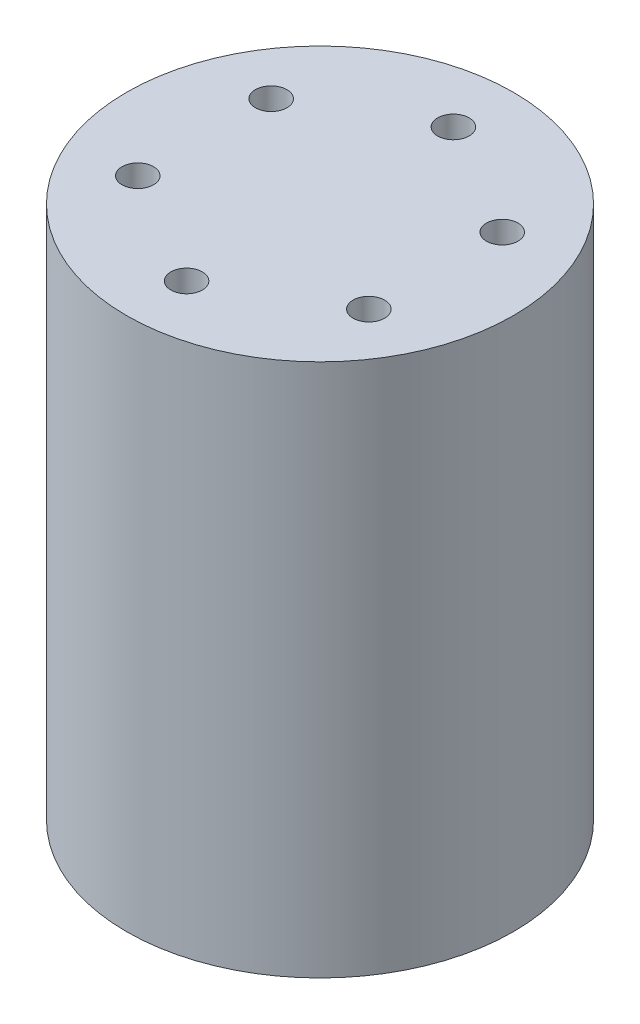
SolidWorks part; units mm, degrees
ref_plane "Front Plane" through (0, 0, 0) normal (0, 0, 1) x (1, 0, 0)
ref_plane "Top Plane" through (0, 0, 0) normal (0, 1, 0) x (1, 0, 0)
ref_plane "Right Plane" through (0, 0, 0) normal (1, 0, 0) x (0, 0, -1)
other "Bounding Box"
ref_plane "Default Plane" through (13.8565, 3.175, 6.7999) normal (0, -1, 0) x (-1, 0, 0)
sketch "Sketch1" plane through (0, 0, 0) normal (0, 1, 0) x (1, 0, 0)
  circle A0 centre (0, 0) radius 18.415
  dimension "D1" = 36.83
extrude "Boss-Extrude1" add sketch "Sketch1" along normal mid plane 50.8
sketch "Sketch2" plane through (0, 25.4, 0) normal (0, 1, 0) x (1, 0, 0)
  line L0 (0, 0) -> (0, 12.7) construction
  circle A0 centre (0, 12.7) radius 1.5
  dimension "D1" = 3
  dimension "D2" = 12.7
extrude "Cut-Extrude1" cut sketch "Sketch2" against normal blind 12.7
pattern_circular "CirPattern1" count 6 over 360 about axis through (0, 0, 0) along (0, 1, 0) of "Cut-Extrude1"
